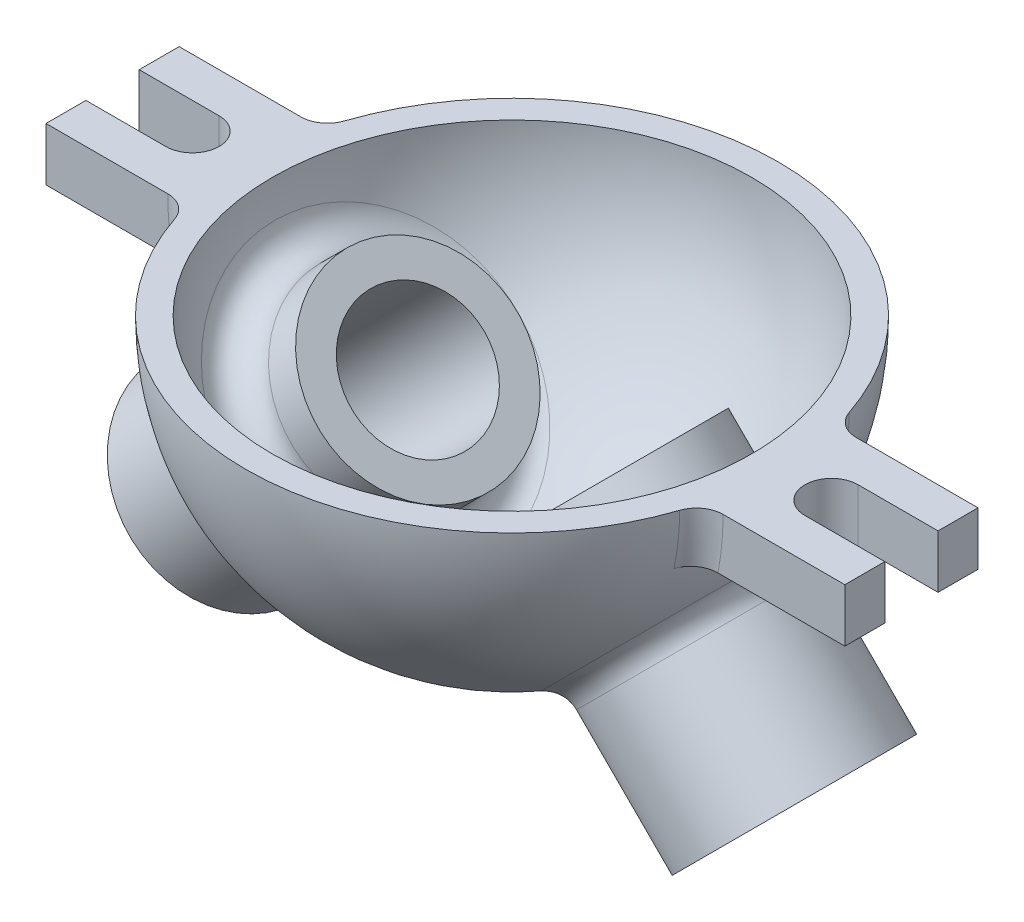
SolidWorks part; units mm, degrees
ref_plane "Front Plane" through (0, 0, 0) normal (0, 0, 1) x (1, 0, 0)
ref_plane "Top Plane" through (0, 0, 0) normal (0, 1, 0) x (1, 0, 0)
ref_plane "Right Plane" through (0, 0, 0) normal (1, 0, 0) x (0, 0, -1)
sketch "Sketch1" plane through (0, 0, 0) normal (0, 1, 0) x (1, 0, 0)
  arc A0 (0, 100) -> (0, -100) centre (0, 0) cw
  dimension "D1" = 100
ref_axis "Axis1" through (0, 0, 100) along (0, 0, -1)
revolve "Revolve-Thin1" add sketch "Sketch1" angle 180 about axis through (0, 0, 100) along (0, 0, -1)
sketch "Sketch3" plane through (0, 0, 0) normal (0, 1, 0) x (1, 0, 0)
  line L0 (96.8246, 25) -> (150, 25) construction
  line L1 (150, 25) -> (150, 10) construction
  line L2 (150, 10) -> (120, 10)
  line L3 (0, -100) -> (0, 100) construction
  line L4 (120, -10) -> (150, -10)
  line L5 (150, -10) -> (150, -25) construction
  line L6 (150, -25) -> (96.8246, -25) construction
  line L7 (0, 100) -> (0, -100) construction
  line L8 (-150, -25) -> (-96.8246, -25) construction
  line L9 (-150, -10) -> (-150, -25) construction
  line L10 (-120, -10) -> (-150, -10)
  line L11 (-150, 10) -> (-120, 10)
  line L12 (-150, 25) -> (-150, 10) construction
  line L13 (-96.8246, 25) -> (-150, 25) construction
  line L14 (-150, 10) -> (-150, -10)
  line L15 (150, 10) -> (150, -10)
  circle A0 centre (0, 0) radius 100 construction
  arc A2 (120, -10) -> (120, 10) centre (120, 0) cw
  arc A3 (-120, -10) -> (-120, 10) centre (-120, 0) ccw
  point P19 (0, 0)
  dimension "D1" = 30
  dimension "D2" = 20
  dimension "D3" = 150
  dimension "D4" = 50
  dimension "D5" = 25
ref_plane "Plane1" through (150, 0, 0) normal (1, 0, 0) x (0, 0, -1)
sketch "Sketch4" plane through (150, 0, 0) normal (1, 0, 0) x (0, 0, -1)
  line L1 (-25, 0) -> (25, 0)
  line L2 (-25, 0) -> (-25, -20)
  line L3 (-25, -20) -> (25, -20)
  line L4 (25, 0) -> (25, -20)
  dimension "D1" = 20
extrude "Boss-Extrude1" add sketch "Sketch4" against normal up to surface (53.1754 mm away)
mirror "Mirror1" about plane through (0, 0, 0) normal (1, 0, 0) of "Boss-Extrude1"
extrude "Cut-Extrude1" cut sketch "Sketch3" against normal up to surface (20 mm away) up to face at (-123.179, -20, 0)
fillet "Fillet1" radius 10 4 edges at (96.3011, -10.0544, -25) (-96.3011, -10.0544, 25) (96.3011, -10.0544, 25) (-96.3011, -10.0544, -25)
sketch "Sketch5" plane through (0, 0, 0) normal (0, 0, 1) x (1, 0, 0)
  line L0 (0, 0) -> (106.066, -106.066) construction
  line L1 (94.803, 0) -> (-94.803, 0) construction
  dimension "D1" = 45
  dimension "D2" = 150
ref_plane "Plane2" through (106.066, -106.066, 0) normal (0.7071, -0.7071, 0) x (0, 0, -1)
sketch "Sketch6" plane through (106.066, -106.066, 0) normal (0.7071, -0.7071, 0) x (0, 0, -1)
  circle A0 centre (0, 0) radius 37.5
  dimension "D1" = 75
extrude "Extrude-Thin1" add sketch "Sketch6" against normal blind 100 thin contours A0 thin type one direction reverse wall 12.5
sketch "Sketch7" plane through (106.066, -106.066, 0) normal (0.7071, -0.7071, 0) x (0, 0, -1)
  circle A0 centre (0, 0) radius 25
  circle A1 centre (0, 0) radius 25 construction
extrude "Cut-Extrude2" cut sketch "Sketch7" against normal blind 100
fillet "Fillet2" radius 10 2 edges at (39.034, -92.0671, 0) (31.3357, -84.3687, 0)
mirror "Mirror2" about plane through (0, 0, 0) normal (1, 0, 0) of "Fillet2", "Cut-Extrude2", "Extrude-Thin1"
